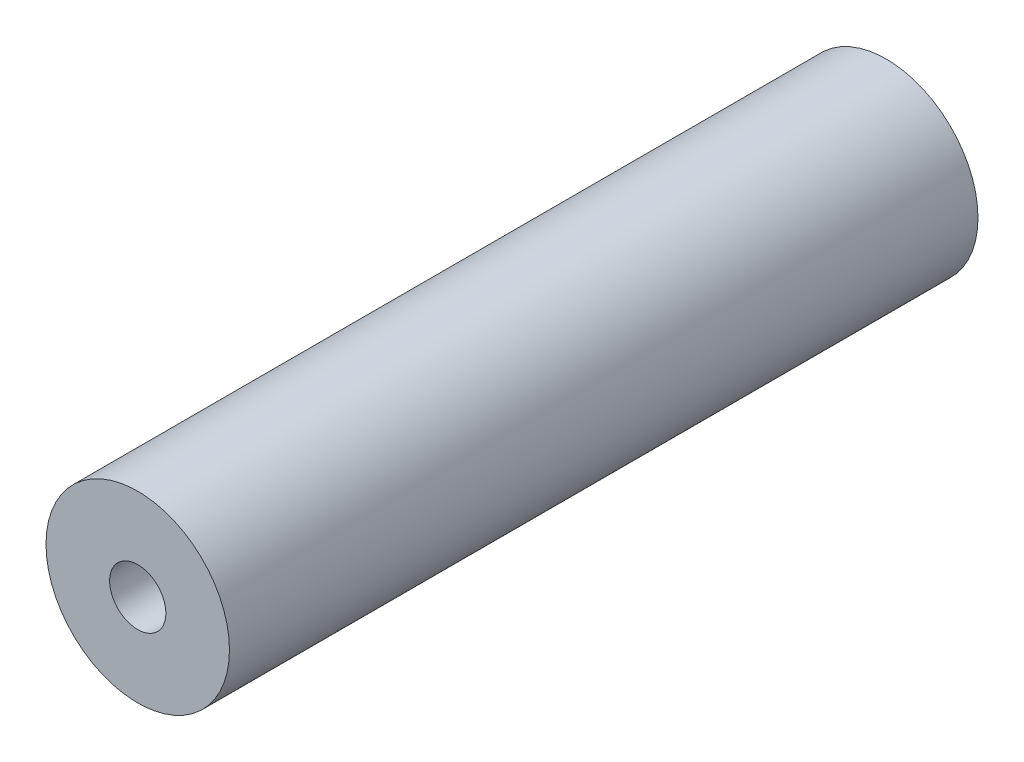
SolidWorks part; units mm, degrees
ref_plane "Front Plane" through (0, 0, 0) normal (0, 0, 1) x (1, 0, 0)
ref_plane "Top Plane" through (0, 0, 0) normal (0, 1, 0) x (1, 0, 0)
ref_plane "Right Plane" through (0, 0, 0) normal (1, 0, 0) x (0, 0, -1)
sketch "Sketch1" plane through (0, 0, 0) normal (0, 0, 1) x (1, 0, 0)
  circle A2 centre (20.0025, 19.685) radius 9.779
  circle A3 centre (20.0025, 19.685) radius 9.779
  dimension "D1" = 0.254
extrude "Boss-Extrude1" add sketch "Sketch1" along normal blind 92.6
sketch "Sketch2" plane through (0, 0, 0) normal (1, 0, 0) x (0, 0, -1)
  line L0 (-92.6, 19.685) -> (7.8089, 19.685) construction
  line L1 (-92.6, 29.464) -> (-92.6, 9.906) construction
  circle A0 centre (-83.583, 19.685) radius 3.4925
  dimension "D1" = 6.985
  dimension "D2" = 9.017
extrude "Cut-Extrude1" cut sketch "Sketch2" along normal through all contours A0
fillet "Fillet1" radius 0.254 2 edges at (10.2398, 19.1211, 80.1363) (29.7652, 20.2489, 80.1363)
fillet "Fillet2" radius 0.254 1 edges at (29.7815, 19.685, 92.6)
sketch "Sketch3" plane through (0, 0, 92.6) normal (0, 0, 1) x (1, 0, 0)
  circle A0 centre (20.0025, 19.685) radius 11.0602
extrude "Cut-Extrude2" cut sketch "Sketch3" against normal blind 12.8016
hole_wizard "M6 Tapped Hole1" positions "3DSketch1" profile "Sketch6" tap size "M6" standard "ISO"
sketch3d "3DSketch1"
  line L0 (20.0025, 19.685, 79.7984) -> (20.0025, 19.685, 0) construction
  point P0 (20.0025, 19.685, 79.7984)
sketch "Sketch6" plane through (20.0025, 19.685, 79.7984) normal (1, 0, 0) x (0, -1, 0)
  line L0 (0, 0) -> (0, 10)
  line L1 (0, 10) -> (2.5, 8.4978)
  line L2 (2.5, 8.4978) -> (2.5, 7)
  line L3 (2.5, 7) -> (3, 7)
  line L4 (3, 7) -> (3, 0)
  line L5 (3, 0) -> (0, 0)
  line L10 (0, 10) -> (-2.5, 8.4978) construction
  line L11 (0, -6.35) -> (0, 107.95) construction
  dimension "Tap Drill Dia." = 5
  dimension "Tap Drill Depth" = 10
  dimension "Thread Major Dia." = 6
  dimension "Thread Depth" = 7
  dimension "Drill Angle" = 118
